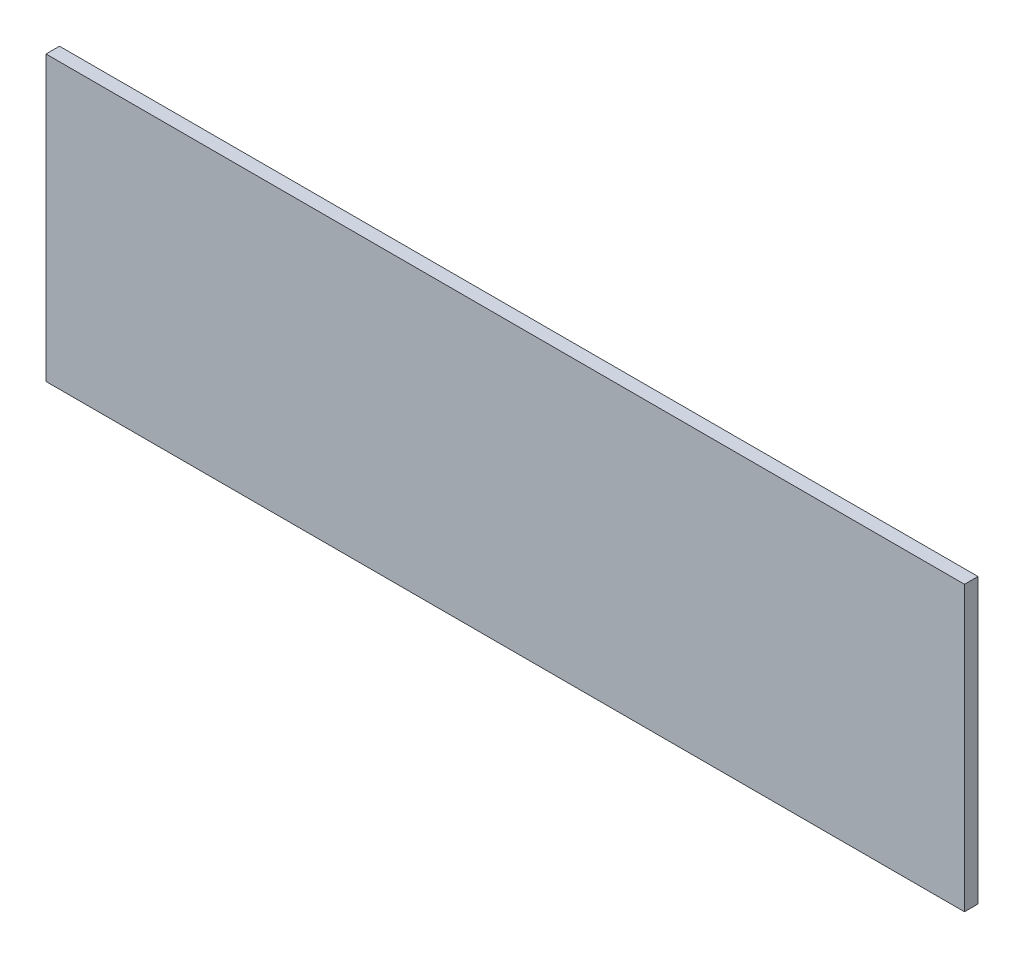
SolidWorks part; units mm, degrees
ref_plane "Plan de face" through (0, 0, 0) normal (0, 0, 1) x (1, 0, 0)
ref_plane "Plan de dessus" through (0, 0, 0) normal (0, 1, 0) x (1, 0, 0)
ref_plane "Plan de droite" through (0, 0, 0) normal (1, 0, 0) x (0, 0, -1)
sketch "Esquisse1" plane through (0, 0, 0) normal (0, 0, 1) x (1, 0, 0)
  line L1 (-340, 105) -> (340, 105)
  line L2 (-340, 105) -> (-340, -105)
  line L3 (-340, -105) -> (340, -105)
  line L4 (340, 105) -> (340, -105)
  dimension "D1" = 680
  dimension "D2" = 210
  dimension "D3" = 105
  dimension "D4" = 340
extrude "Boss.-Extru.1" add sketch "Esquisse1" along normal blind 10
